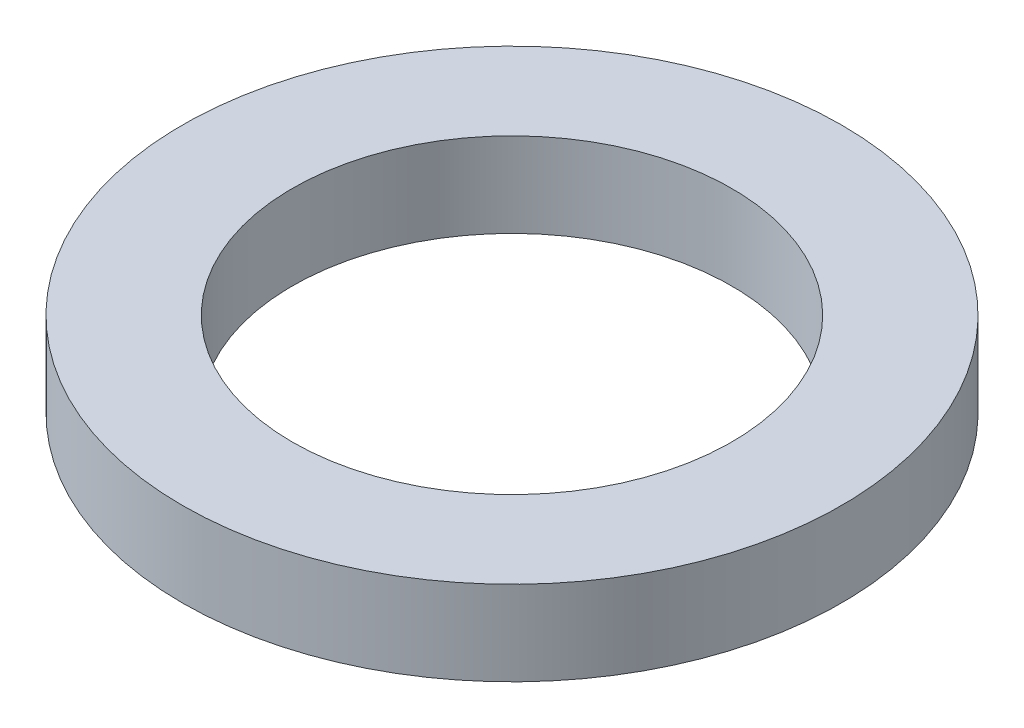
SolidWorks part; units mm, degrees
material "1.0553 (S355J0)"
ref_plane "Płaszczyzna przednia" through (0, 0, 0) normal (0, 0, 1) x (1, 0, 0)
ref_plane "Płaszczyzna górna" through (0, 0, 0) normal (0, 1, 0) x (1, 0, 0)
ref_plane "Płaszczyzna prawa" through (0, 0, 0) normal (1, 0, 0) x (0, 0, -1)
sketch "Szkic1" plane through (0, 0, 0) normal (0, 1, 0) x (1, 0, 0)
  circle A0 centre (0, 0) radius 9.75
  circle A1 centre (0, 0) radius 6.5
  dimension "D1" = 13
  dimension "D2" = 19.5
extrude "Dodanie-wyciągnięcie1" add sketch "Szkic1" along normal blind 2.5
